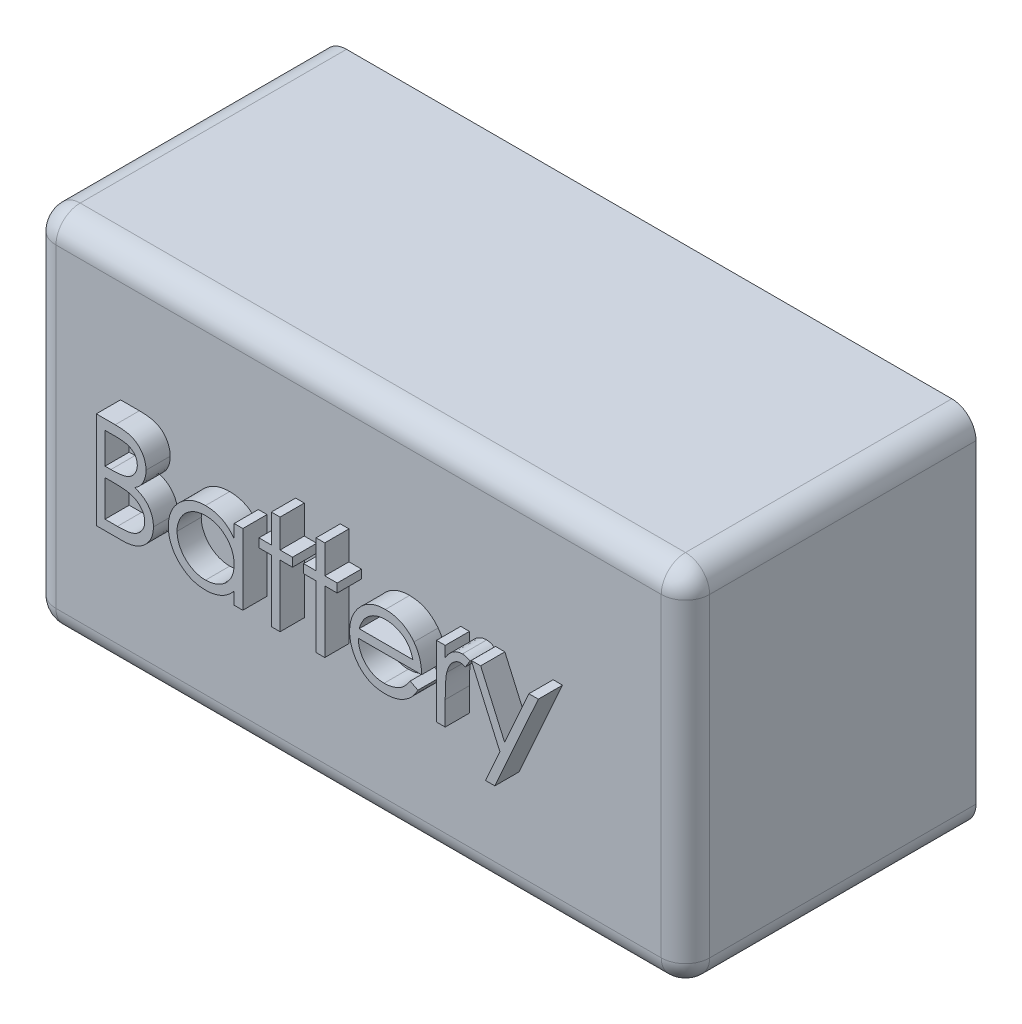
SolidWorks part; units mm, degrees
ref_plane "Front Plane" through (0, 0, 0) normal (0, 0, 1) x (1, 0, 0)
ref_plane "Top Plane" through (0, 0, 0) normal (0, 1, 0) x (1, 0, 0)
ref_plane "Right Plane" through (0, 0, 0) normal (1, 0, 0) x (0, 0, -1)
sketch "Sketch1" plane through (0, 0, 0) normal (0, 0, 1) x (1, 0, 0)
  line L1 (-67.5, -37.5) -> (67.5, -37.5)
  line L2 (-67.5, -37.5) -> (-67.5, 37.5)
  line L3 (-67.5, 37.5) -> (67.5, 37.5)
  line L4 (67.5, -37.5) -> (67.5, 37.5)
  line L5 (0, 37.5) -> (0, -37.5) construction
  line L6 (-67.5, 0) -> (67.5, 0) construction
  point P0 (0, 0)
  dimension "D1" = 135
  dimension "D2" = 75
extrude "Boss-Extrude1" add sketch "Sketch1" along normal blind 60
fillet "Fillet2" radius 5 3 edges at (67.5, 0, 60) (67.5, 37.5, 30) (0, 37.5, 60)
sketch "Sketch2" plane through (0, 0, 60) normal (0, 0, 1) x (1, 0, 0)
  text T0 "Battery" font "Century Gothic" height 20
extrude "Boss-Extrude2" add sketch "Sketch2" along normal blind 5
fillet "Fillet4" radius 5 3 edges at (-2.5, -37.5, 60) (66.0355, -37.5, 58.5355) (67.5, -37.5, 27.5)
fillet "Fillet5" radius 5 5 edges at (-67.5, 37.5, 27.5) (-67.5, 36.0355, 58.5355) (-67.5, 0, 60) (-67.5, -36.0355, 58.5355) (-67.5, -37.5, 27.5)
